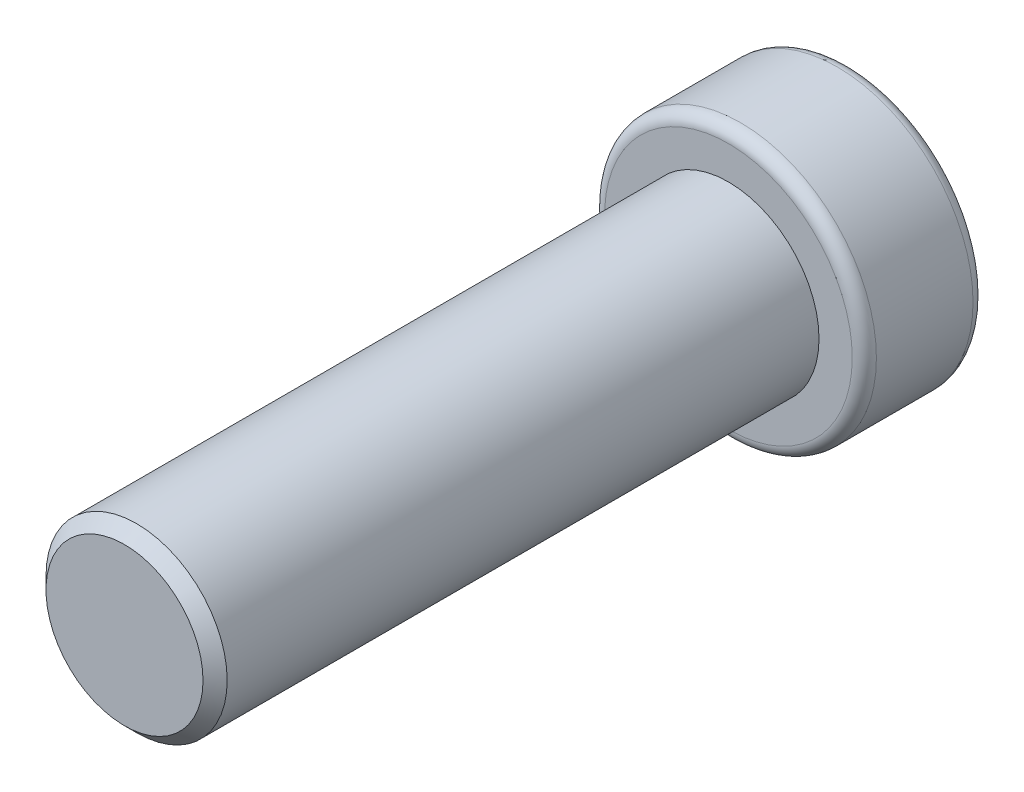
SolidWorks part; units mm, degrees
ref_plane "Front Plane" through (0, 0, 0) normal (0, 0, 1) x (1, 0, 0)
ref_plane "Top Plane" through (0, 0, 0) normal (0, 1, 0) x (1, 0, 0)
ref_plane "Right Plane" through (0, 0, 0) normal (1, 0, 0) x (0, 0, -1)
sketch "Sketch1" plane through (0, 0, 0) normal (0, 1, 0) x (1, 0, 0)
  line L0 (0, 0) -> (0, 18.777) construction
  line L1 (0, 12) -> (2.05, 12)
  line L2 (2.25, 11.8) -> (2.25, 10.2)
  line L3 (2.05, 10) -> (1.5, 10)
  line L4 (1.5, 10) -> (1.5, 0.2)
  line L5 (1.3, 0) -> (0, 0)
  line L6 (0, 0) -> (0, 12)
  line L7 (1.5, 0.2) -> (1.3, 0)
  arc A0 (2.25, 10.2) -> (2.05, 10) centre (2.05, 10.2) cw
  arc A1 (2.25, 11.8) -> (2.05, 12) centre (2.05, 11.8) ccw
  point P8 (1.5, 0)
  point P10 (2.25, 10)
  point P13 (2.25, 12)
  dimension "D5" = 0.2
  dimension "D1" = 2
  dimension "D2" = 3
  dimension "D3" = 10
  dimension "D4" = 4.5
revolve "Revolve1" add sketch "Sketch1" angle 360 about L0
sketch "Sketch2" plane through (0, 0, -12) normal (0, 0, -1) x (-1, 0, 0)
  line L1 (1.25, 0.7217) -> (0, 1.4434)
  line L2 (0, 1.4434) -> (-1.25, 0.7217)
  line L3 (-1.25, 0.7217) -> (-1.25, -0.7217)
  line L4 (-1.25, -0.7217) -> (0, -1.4434)
  line L5 (0, -1.4434) -> (1.25, -0.7217)
  line L6 (1.25, -0.7217) -> (1.25, 0.7217)
  circle A0 centre (0, 0) radius 1.25 construction
  dimension "D1" = 2.5
extrude "Cut-Extrude1" cut sketch "Sketch2" against normal blind 1.5
chamfer "Chamfer1" distance 0.2 angle 45 6 edges at (-0.625, -1.0825, -10.5) (0.625, -1.0825, -10.5) (1.25, 0, -10.5) (0.625, 1.0825, -10.5) (-0.625, 1.0825, -10.5) (-1.25, 0, -10.5)
